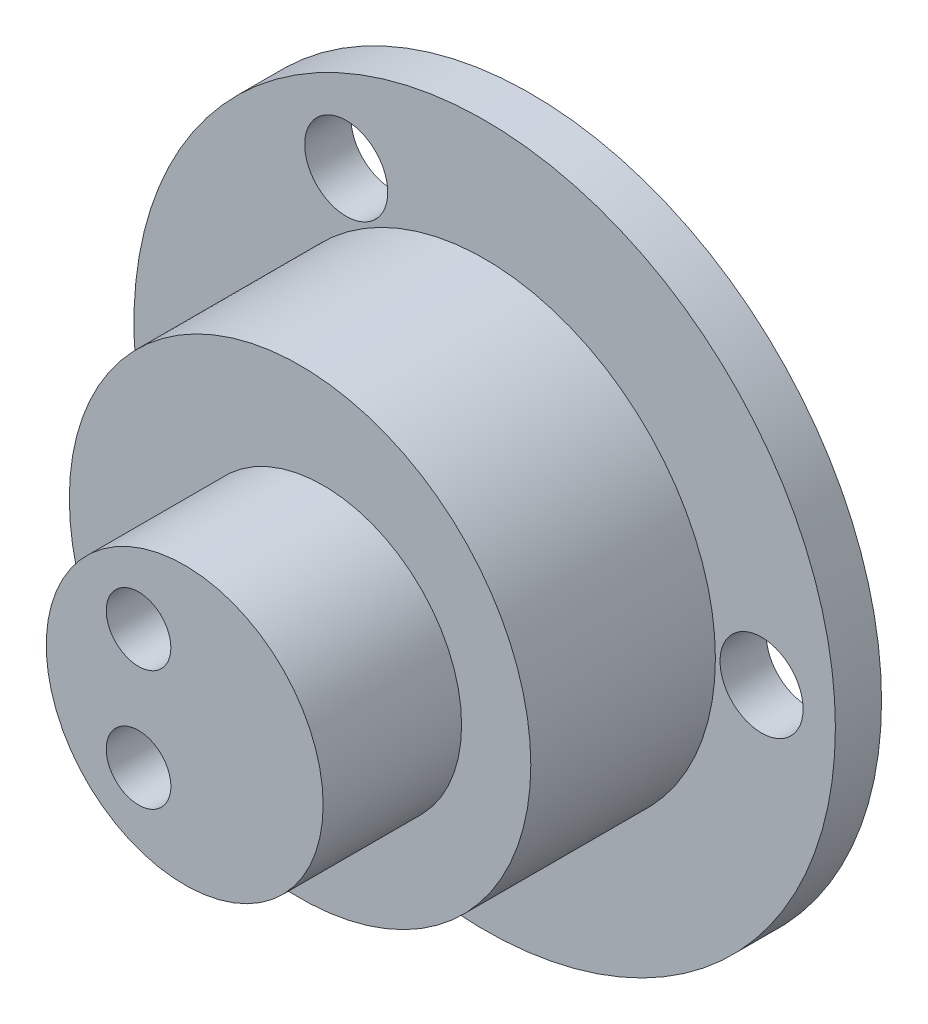
SolidWorks part; units mm, degrees
ref_plane "前视基准面" through (0, 0, 0) normal (0, 0, 1) x (1, 0, 0)
ref_plane "上视基准面" through (0, 0, 0) normal (0, 1, 0) x (1, 0, 0)
ref_plane "右视基准面" through (0, 0, 0) normal (1, 0, 0) x (0, 0, -1)
sketch "草图1" plane through (0, 0, 0) normal (0, 0, 1) x (1, 0, 0)
  circle A0 centre (6, 0) radius 0.9
  circle A1 centre (-3, -5.1962) radius 0.9
  circle A2 centre (-3, 5.1962) radius 0.9
  circle A3 centre (0, 0) radius 4.45
  circle A4 centre (0, 0) radius 7.5
  point P7 (0, 0)
extrude "凸台-拉伸1" add sketch "草图1" along normal blind 1
sketch "草图2" plane through (0, 0, 1) normal (0, 0, 1) x (1, 0, 0)
  circle A0 centre (0, 0) radius 5
extrude "凸台-拉伸2" add sketch "草图2" along normal blind 4
sketch "草图3" plane through (0, 0, 1) normal (0, 0, -1) x (-1, 0, 0)
  circle A1 centre (0, 0) radius 4.45
  circle A2 centre (0, 0) radius 4.45
  dimension "D1" = 0
extrude "切除-拉伸1" cut sketch "草图3" against normal blind 1
sketch "草图4" plane through (0, 0, 5) normal (0, 0, 1) x (1, 0, 0)
  line L0 (0, 0) -> (0.5, 0)
sketch "草图5" plane through (0, 0, 5) normal (0, 0, 1) x (1, 0, 0)
  circle A0 centre (0.5, 0) radius 3
extrude "凸台-拉伸4" add sketch "草图5" along normal blind 3
sketch "草图6" plane through (0, 0, 1) normal (0, 0, 1) x (1, 0, 0)
  circle A0 centre (0, 0) radius 9
  circle A1 centre (-3, -5.1962) radius 0.9 construction
  circle A2 centre (-3, 5.1962) radius 0.9 construction
  circle A3 centre (6, 0) radius 0.9 construction
  circle A4 centre (6, 0) radius 0.9
  circle A5 centre (-3, 5.1962) radius 0.9
  circle A6 centre (-3, -5.1962) radius 0.9
  circle A7 centre (0, 0) radius 4.45
extrude "凸台-拉伸7" add sketch "草图6" against normal up to surface (1 mm away) up to face at (7.5, 0, 0)
sketch "草图7" plane through (0, 0, 8) normal (0, 0, 1) x (1, 0, 0)
  circle A2 centre (-0.5, 1.3) radius 0.7
  circle A3 centre (-0.5, -1.3) radius 0.7
  point P4 (-0.5, 1.5)
  point P9 (-0.5, 0)
extrude "切除-拉伸2" cut sketch "草图7" against normal blind 10
sketch "草图8" plane through (0, 0, 1) normal (0, 0, 1) x (1, 0, 0)
  circle A0 centre (0, 0) radius 7.6
  circle A1 centre (0, 0) radius 9 construction
  circle A2 centre (0, 0) radius 9
extrude "切除-拉伸3" cut sketch "草图8" against normal blind 10
